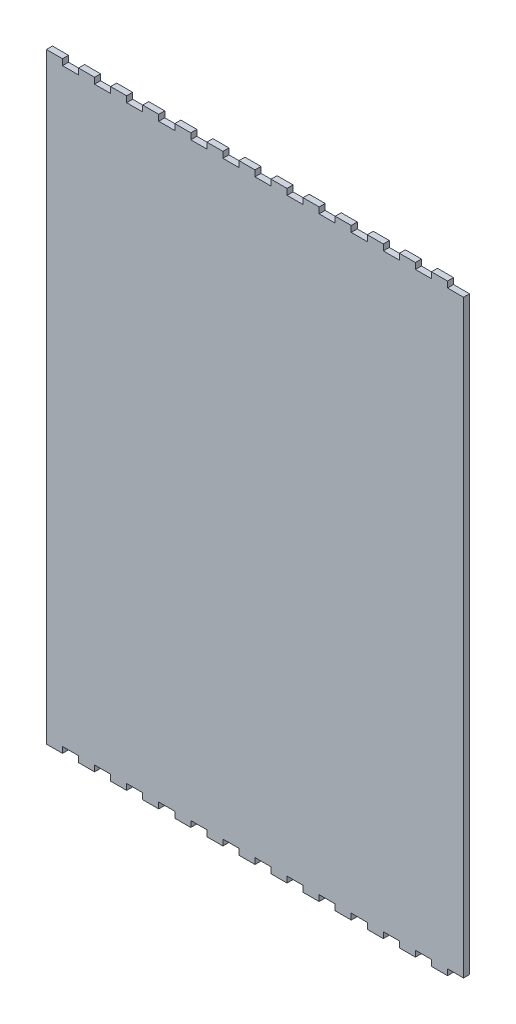
SolidWorks part; units mm, degrees
ref_plane "Plan de face" through (0, 0, 0) normal (0, 0, 1) x (1, 0, 0)
ref_plane "Plan de dessus" through (0, 0, 0) normal (0, 1, 0) x (1, 0, 0)
ref_plane "Plan de droite" through (0, 0, 0) normal (1, 0, 0) x (0, 0, -1)
sketch "Esquisse1" plane through (0, 0, 0) normal (0, 0, 1) x (1, 0, 0)
  line L1 (-104, 150) -> (104, 150)
  line L2 (-104, 150) -> (-104, -150)
  line L3 (-104, -150) -> (104, -150)
  line L4 (104, 150) -> (104, -150)
  line L5 (-104, 150) -> (104, -150) construction
  line L6 (-104, -150) -> (104, 150) construction
  point P0 (0, 0)
  dimension "D1" = 208
  dimension "D2" = 300
extrude "Boss.-Extru.1" add sketch "Esquisse1" along normal blind 3
sketch "Esquisse2" plane through (0, 0, 3) normal (0, 0, 1) x (1, 0, 0)
  line L0 (104, 150) -> (-104, 150) construction
  line L1 (-96, 150) -> (-88, 150)
  line L2 (-96, 150) -> (-96, 147)
  line L3 (-96, 147) -> (-88, 147)
  line L4 (-88, 150) -> (-88, 147)
  line L5 (-104, 150) -> (-104, -150) construction
  line L6 (-80, 150) -> (-80, 147)
  line L7 (-80, 150) -> (-72, 150)
  line L8 (-72, 150) -> (-72, 147)
  line L9 (-80, 147) -> (-72, 147)
  line L10 (-64, 150) -> (-64, 147)
  line L11 (-64, 150) -> (-56, 150)
  line L12 (-56, 150) -> (-56, 147)
  line L13 (-64, 147) -> (-56, 147)
  line L14 (-48, 150) -> (-48, 147)
  line L15 (-48, 150) -> (-40, 150)
  line L16 (-40, 150) -> (-40, 147)
  line L17 (-48, 147) -> (-40, 147)
  line L18 (-32, 150) -> (-32, 147)
  line L19 (-32, 150) -> (-24, 150)
  line L20 (-24, 150) -> (-24, 147)
  line L21 (-32, 147) -> (-24, 147)
  line L22 (-16, 150) -> (-16, 147)
  line L23 (-16, 150) -> (-8, 150)
  line L24 (-8, 150) -> (-8, 147)
  line L25 (-16, 147) -> (-8, 147)
  line L26 (0, 150) -> (0, 147)
  line L27 (0, 150) -> (8, 150)
  line L28 (8, 150) -> (8, 147)
  line L29 (0, 147) -> (8, 147)
  line L30 (16, 150) -> (16, 147)
  line L31 (16, 150) -> (24, 150)
  line L32 (24, 150) -> (24, 147)
  line L33 (16, 147) -> (24, 147)
  line L34 (32, 150) -> (32, 147)
  line L35 (32, 150) -> (40, 150)
  line L36 (40, 150) -> (40, 147)
  line L37 (32, 147) -> (40, 147)
  line L38 (48, 150) -> (48, 147)
  line L39 (48, 150) -> (56, 150)
  line L40 (56, 150) -> (56, 147)
  line L41 (48, 147) -> (56, 147)
  line L42 (64, 150) -> (64, 147)
  line L43 (64, 150) -> (72, 150)
  line L44 (72, 150) -> (72, 147)
  line L45 (64, 147) -> (72, 147)
  line L46 (80, 150) -> (80, 147)
  line L47 (80, 150) -> (88, 150)
  line L48 (88, 150) -> (88, 147)
  line L49 (80, 147) -> (88, 147)
  line L50 (96, 150) -> (96, 147)
  line L51 (96, 150) -> (104, 150)
  line L52 (104, 150) -> (104, 147)
  line L53 (96, 147) -> (104, 147)
  line L54 (-104, 0) -> (104, 0) construction
  line L55 (104, -150) -> (104, 150) construction
  line L56 (96, -147) -> (104, -147)
  line L57 (104, -150) -> (104, -147)
  line L58 (96, -150) -> (104, -150)
  line L59 (96, -150) -> (96, -147)
  line L60 (80, -147) -> (88, -147)
  line L61 (88, -150) -> (88, -147)
  line L62 (80, -150) -> (88, -150)
  line L63 (80, -150) -> (80, -147)
  line L64 (64, -147) -> (72, -147)
  line L65 (72, -150) -> (72, -147)
  line L66 (64, -150) -> (72, -150)
  line L67 (64, -150) -> (64, -147)
  line L68 (48, -147) -> (56, -147)
  line L69 (56, -150) -> (56, -147)
  line L70 (48, -150) -> (56, -150)
  line L71 (48, -150) -> (48, -147)
  line L72 (32, -147) -> (40, -147)
  line L73 (40, -150) -> (40, -147)
  line L74 (32, -150) -> (40, -150)
  line L75 (32, -150) -> (32, -147)
  line L76 (16, -147) -> (24, -147)
  line L77 (24, -150) -> (24, -147)
  line L78 (16, -150) -> (24, -150)
  line L79 (16, -150) -> (16, -147)
  line L80 (0, -147) -> (8, -147)
  line L81 (8, -150) -> (8, -147)
  line L82 (0, -150) -> (8, -150)
  line L83 (0, -150) -> (0, -147)
  line L84 (-16, -147) -> (-8, -147)
  line L85 (-8, -150) -> (-8, -147)
  line L86 (-16, -150) -> (-8, -150)
  line L87 (-16, -150) -> (-16, -147)
  line L88 (-32, -147) -> (-24, -147)
  line L89 (-24, -150) -> (-24, -147)
  line L90 (-32, -150) -> (-24, -150)
  line L91 (-32, -150) -> (-32, -147)
  line L92 (-48, -147) -> (-40, -147)
  line L93 (-40, -150) -> (-40, -147)
  line L94 (-48, -150) -> (-40, -150)
  line L95 (-48, -150) -> (-48, -147)
  line L96 (-64, -147) -> (-56, -147)
  line L97 (-56, -150) -> (-56, -147)
  line L98 (-64, -150) -> (-56, -150)
  line L99 (-64, -150) -> (-64, -147)
  line L100 (-80, -147) -> (-72, -147)
  line L101 (-72, -150) -> (-72, -147)
  line L102 (-80, -150) -> (-72, -150)
  line L103 (-80, -150) -> (-80, -147)
  line L104 (-88, -150) -> (-88, -147)
  line L105 (-96, -147) -> (-88, -147)
  line L106 (-96, -150) -> (-96, -147)
  line L107 (-96, -150) -> (-88, -150)
  dimension "D1" = 8
  dimension "D2" = 3
  dimension "D3" = 8
  dimension "D5" = 8
  dimension "D4" = 13
extrude "Enlèv. mat.-Extru.1" cut sketch "Esquisse2" against normal blind 3
